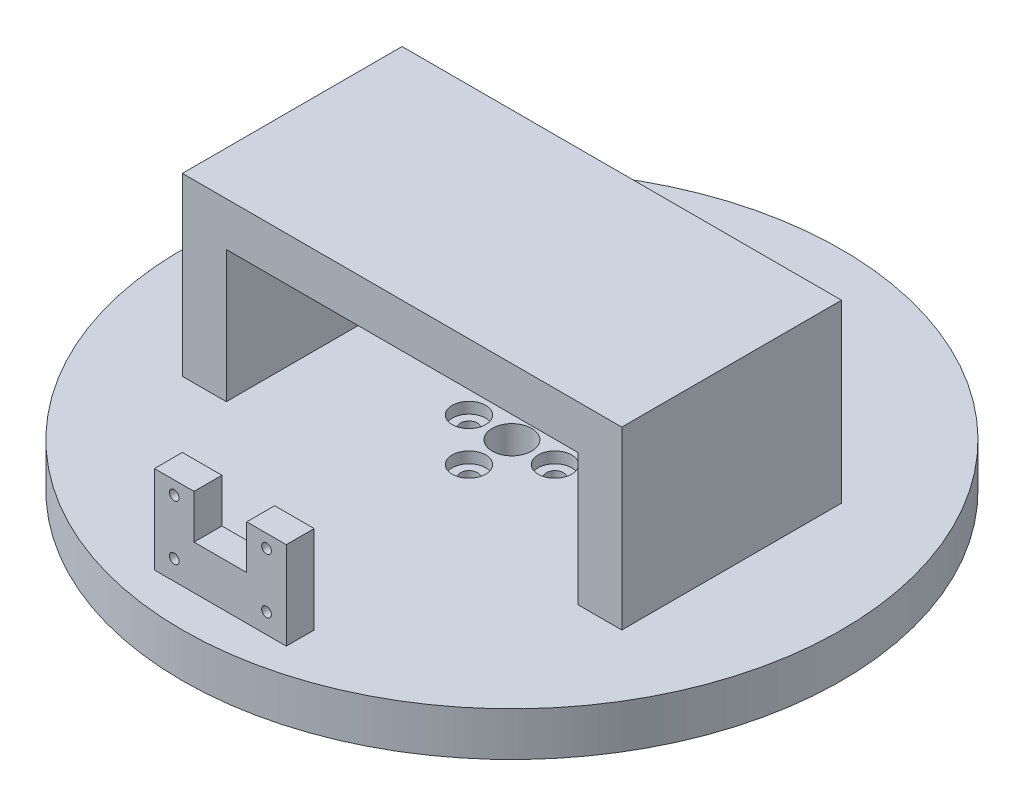
SolidWorks part; units mm, degrees
material "ABS"
ref_plane "Front Plane" through (0, 0, 0) normal (0, 0, 1) x (1, 0, 0)
ref_plane "Top Plane" through (0, 0, 0) normal (0, 1, 0) x (1, 0, 0)
ref_plane "Right Plane" through (0, 0, 0) normal (1, 0, 0) x (0, 0, -1)
sketch "Sketch1" plane through (0, 0, 0) normal (0, 1, 0) x (1, 0, 0)
  circle A0 centre (0, 0) radius 75
  dimension "D1" = 150
extrude "Boss-Extrude1" add sketch "Sketch1" along normal blind 10
sketch "Sketch2" plane through (0, 10, 0) normal (0, 1, 0) x (1, 0, 0)
  circle A0 centre (0, 0) radius 9.779
  circle A1 centre (0, 9.779) radius 1.905
  dimension "D1" = 19.558
  dimension "D2" = 3.81
extrude "Cut-Extrude2" cut sketch "Sketch2" against normal through all contours A0 A1 | A0 A1
pattern_circular "CirPattern1" count 4 every 90 about axis through (0, 0, 0) along (0, 1, 0) of "Cut-Extrude2"
sketch "Sketch3" plane through (0, 10, 0) normal (0, 1, 0) x (1, 0, 0)
  circle A0 centre (0, 0) radius 4.5
  dimension "D1" = 9
extrude "Cut-Extrude3" cut sketch "Sketch3" against normal through all
sketch "Sketch4" plane through (0, 10, 0) normal (0, 1, 0) x (1, 0, 0)
  circle A0 centre (0, 9.779) radius 3.81
  dimension "D1" = 7.62
extrude "Cut-Extrude4" cut sketch "Sketch4" against normal blind 2.54
pattern_circular "CirPattern2" count 4 every 90 about axis through (0, 0, 0) along (0, 1, 0) of "Cut-Extrude4"
sketch "Sketch5" plane through (0, 10, 0) normal (0, 1, 0) x (1, 0, 0)
  line L1 (-40, -25) -> (-50, -25)
  line L2 (-40, -25) -> (-40, 25)
  line L3 (-40, 25) -> (-50, 25)
  line L4 (-50, -25) -> (-50, 25)
  line L5 (-40, -25) -> (-50, 25) construction
  line L6 (-40, 25) -> (-50, -25) construction
  point P0 (-45, 0)
  dimension "D1" = 10
  dimension "D2" = 50
  dimension "D3" = 40
extrude "Boss-Extrude2" add sketch "Sketch5" along normal blind 40
sketch "Sketch6" plane through (-40, 0, 0) normal (1, 0, 0) x (0, 0, -1)
  line L0 (25, 50) -> (25, 10) construction
  line L1 (-25, 50) -> (25, 50)
  line L2 (-25, 50) -> (-25, 40)
  line L3 (-25, 40) -> (25, 40)
  line L4 (25, 50) -> (25, 40)
  dimension "D1" = 10
extrude "Boss-Extrude3" add sketch "Sketch6" along normal blind 40
mirror "Mirror1" about plane through (0, 0, 0) normal (1, 0, 0) of "Boss-Extrude3", "Boss-Extrude2"
sketch "Sketch7" plane through (0, 10, 0) normal (0, 1, 0) x (1, 0, 0)
  line L1 (15, -66.35) -> (-15, -66.35)
  line L2 (15, -66.35) -> (15, -60)
  line L3 (15, -60) -> (-15, -60)
  line L4 (-15, -66.35) -> (-15, -60)
  line L5 (15, -66.35) -> (-15, -60) construction
  line L6 (15, -60) -> (-15, -66.35) construction
  point P0 (0, -63.175)
  dimension "D1" = 30
  dimension "D2" = 6.35
  dimension "D3" = 60
extrude "Boss-Extrude4" add sketch "Sketch7" along normal blind 20
sketch "Sketch8" plane through (0, 0, 66.35) normal (0, 0, 1) x (1, 0, 0)
  line L0 (15, 30) -> (15, 10) construction
  line L1 (-15, 30) -> (15, 30) construction
  line L2 (-15, 30) -> (-15, 10) construction
  line L4 (6, 20) -> (-6, 20)
  line L5 (6, 20) -> (6, 40)
  line L6 (6, 40) -> (-6, 40)
  line L7 (-6, 20) -> (-6, 40)
  line L8 (6, 20) -> (-6, 40) construction
  line L9 (6, 40) -> (-6, 20) construction
  circle A1 centre (-10.5, 27) radius 1.1
  circle A2 centre (-10.5, 14.5) radius 1.1
  circle A4 centre (10.5, 27) radius 1.1
  circle A5 centre (10.5, 14.5) radius 1.1
  point P10 (0, 30)
  point P17 (0, 0)
  point P20 (0, 0)
  point P22 (-39.7134, 40)
  dimension "D1" = 3
  dimension "D2" = 4.5
  dimension "D4" = 12
  dimension "D5" = 2.2
  dimension "D6" = 2.2
  dimension "D7" = 2.2
  dimension "D8" = 2.2
  dimension "D10" = 4.5
  dimension "D3" = 15.5
  dimension "D9" = 20
extrude "Cut-Extrude5" cut sketch "Sketch8" against normal up to next
